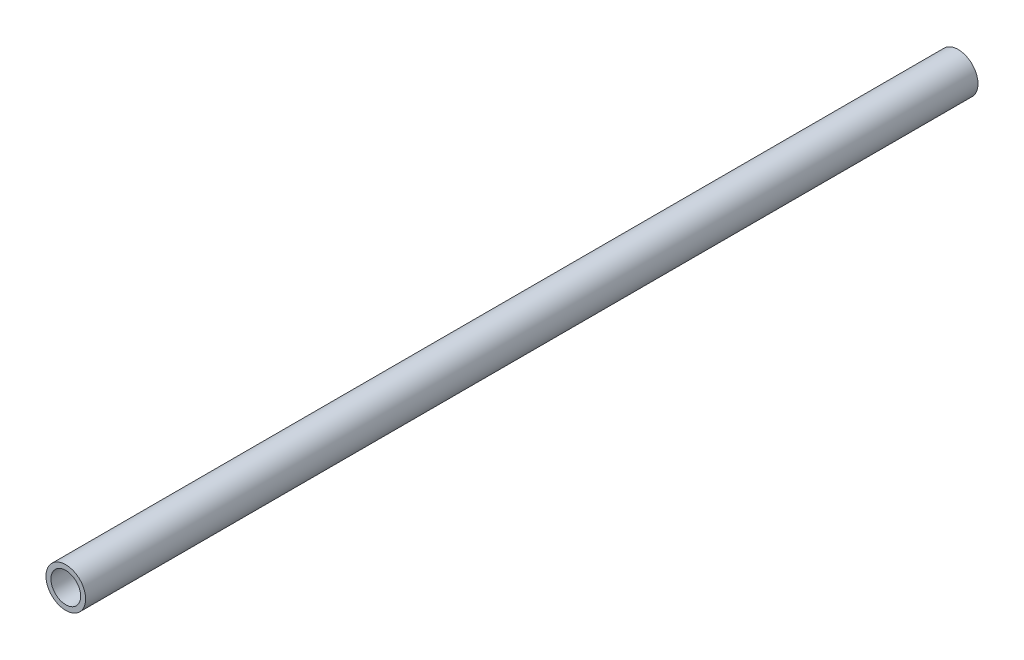
SolidWorks part; units mm, degrees
ref_plane "前视基准面" through (0, 0, 0) normal (0, 0, 1) x (1, 0, 0)
ref_plane "上视基准面" through (0, 0, 0) normal (0, 1, 0) x (1, 0, 0)
ref_plane "右视基准面" through (0, 0, 0) normal (1, 0, 0) x (0, 0, -1)
sketch "草图1" plane through (0, 0, 0) normal (0, 0, 1) x (1, 0, 0)
  circle A0 centre (0, 0) radius 3
  circle A1 centre (0, 0) radius 4
  dimension "D1" = 6
  dimension "D2" = 8
extrude "凸台-拉伸1" add sketch "草图1" along normal blind 180
